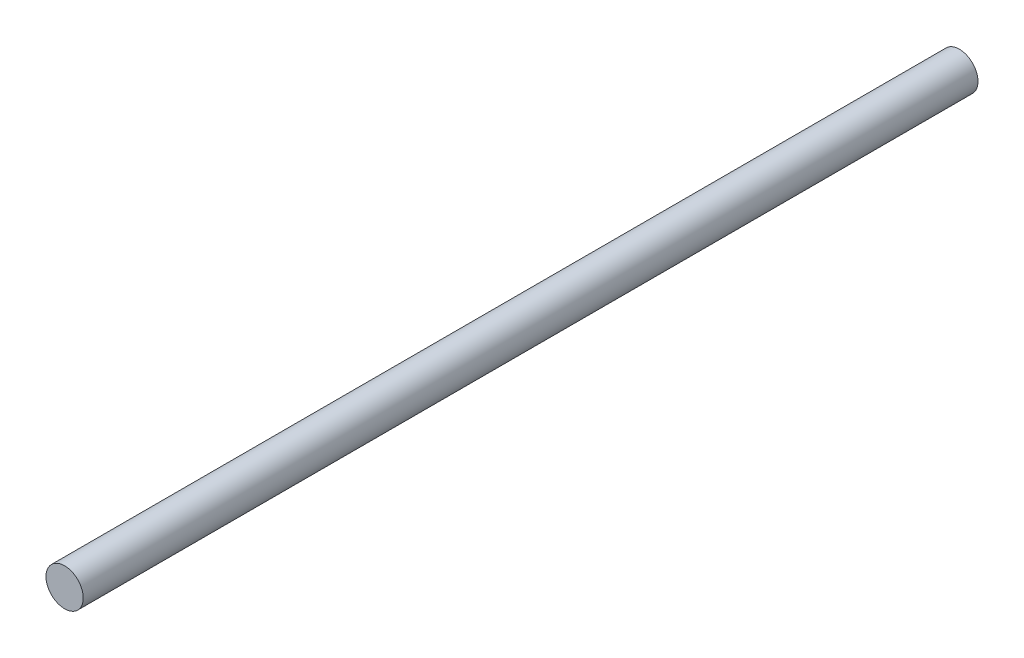
SolidWorks part; units mm, degrees
ref_plane "Front Plane" through (0, 0, 0) normal (0, 0, 1) x (1, 0, 0)
ref_plane "Top Plane" through (0, 0, 0) normal (0, 1, 0) x (1, 0, 0)
ref_plane "Right Plane" through (0, 0, 0) normal (1, 0, 0) x (0, 0, -1)
sketch "Sketch1" plane through (0, 0, 0) normal (0, 0, 1) x (1, 0, 0)
  circle A0 centre (0, 0) radius 1
  dimension "D1" = 2
extrude "Boss-Extrude1" add sketch "Sketch1" along normal blind 48 contours A0
